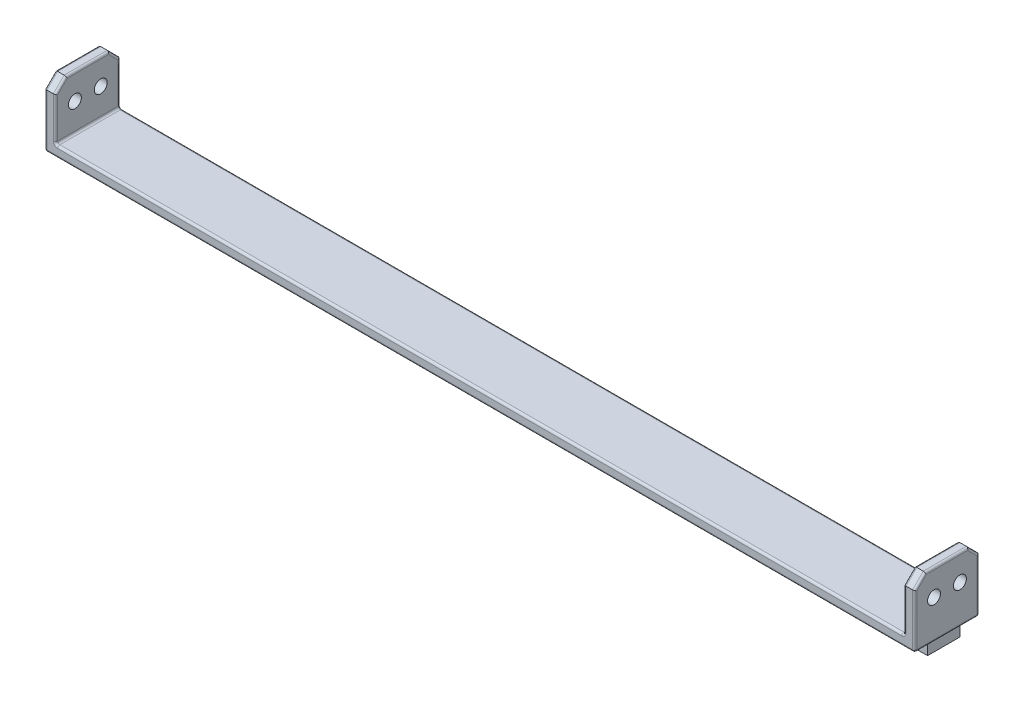
SolidWorks part; units mm, degrees
ref_plane "Front Plane" through (0, 0, 0) normal (0, 0, 1) x (1, 0, 0)
ref_plane "Top Plane" through (0, 0, 0) normal (0, 1, 0) x (1, 0, 0)
ref_plane "Right Plane" through (0, 0, 0) normal (1, 0, 0) x (0, 0, -1)
sketch "Sketch1" plane through (0, 0, 0) normal (0, 0, 1) x (1, 0, 0)
  line L0 (-201.93, 0) -> (201.93, 0)
  line L1 (-201.93, 0) -> (-201.93, 30)
  line L2 (201.93, 0) -> (201.93, 30)
  point P4 (0, 0)
  dimension "D1" = 403.86
  dimension "D2" = 30
extrude "Extrude-Thin1" add sketch "Sketch1" against normal blind 30 thin thin type one direction reverse wall 5
chamfer "Chamfer1" distance 5 angle 45 4 edges at (199.43, 30, -30) (199.43, 30, 0) (-199.43, 30, -30) (-199.43, 30, 0)
fillet "Fillet1" radius 1 28 edges at (-201.93, 27.5, -2.5) (-201.93, 12.5, 0) (-201.93, 12.5, -30) (-201.93, 27.5, -27.5) (-201.93, 30, -15) (0, 0, -30) (-201.93, 0, -15) (0, 0, 0) (201.93, 0, -15) (201.93, 12.5, 0) (201.93, 27.5, -2.5) (201.93, 30, -15) (201.93, 27.5, -27.5) (201.93, 12.5, -30) (196.93, 27.5, -2.5) (196.93, 15, 0) (196.93, 15, -30) (196.93, 27.5, -27.5) (196.93, 30, -15) (-196.93, 15, 0) (-196.93, 27.5, -2.5) (-196.93, 30, -15) (-196.93, 27.5, -27.5) (-196.93, 15, -30) (-196.93, 5, -15) (0, 5, -30) (196.93, 5, -15) (0, 5, 0)
hole_wizard "Ø6.0mm Dowel Slot1" positions "Sketch3" profile "Sketch4" size "Ø6.0" standard "ANSI Metric" slot yes end condition through all
sketch "Sketch3" plane through (201.93, 0, 0) normal (1, 0, 0) x (0, 0, -1)
  line L1 (15, 0) -> (15, 12.1789) construction
  line L2 (29, 0) -> (1, 0) construction
  point P0 (21, 18)
  point P4 (9, 18)
  dimension "D2" = 12
  dimension "D3" = 18
sketch "Sketch4" plane through (201.93, 18, -21) normal (0, 1, 0) x (0, 0, -1)
  line L0 (0, 0) -> (0, 403.86)
  line L1 (0, 403.86) -> (3, 403.86)
  line L2 (3, 403.86) -> (3, 0)
  line L5 (3, 0) -> (0, 0)
  line L11 (0, -6.35) -> (0, 107.95) construction
  dimension "Thru Hole Dia." = 6
  dimension "Thru Hole Depth" = 403.86
sketch "Sketch6" plane through (0, 0, 0) normal (0, -1, 0) x (1, 0, 0)
  line L0 (-200.93, -1) -> (-200.93, -29) construction
  line L1 (-200.93, -7) -> (200.93, -7)
  line L2 (-200.93, -7) -> (-200.93, -22)
  line L3 (-200.93, -22) -> (200.93, -22)
  line L4 (200.93, -7) -> (200.93, -22)
  line L5 (200.93, -29) -> (200.93, -1) construction
  line L6 (200.93, -14.5) -> (171.1265, -14.5) construction
  line L7 (-200.93, 0) -> (200.93, 0) construction
  dimension "D1" = 15
  dimension "D2" = 7
extrude "Boss-Extrude1" add sketch "Sketch6" along normal blind 5 separate body
